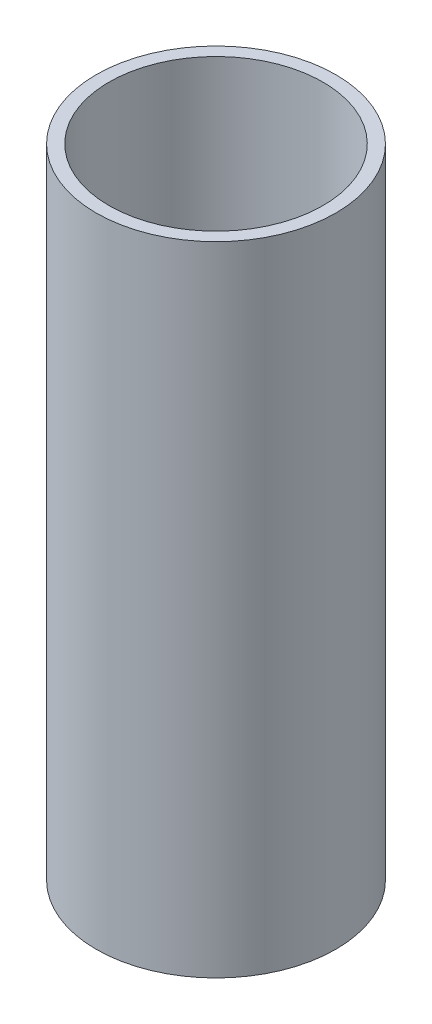
SolidWorks part; units mm, degrees
ref_plane "Front Plane" through (0, 0, 0) normal (0, 0, 1) x (1, 0, 0)
ref_plane "Top Plane" through (0, 0, 0) normal (0, 1, 0) x (1, 0, 0)
ref_plane "Right Plane" through (0, 0, 0) normal (1, 0, 0) x (0, 0, -1)
sketch "Sketch1" plane through (0, 0, 0) normal (0, 1, 0) x (1, 0, 0)
  circle A0 centre (0, 0) radius 14
  circle A1 centre (0, 0) radius 12.5
extrude "Boss-Extrude1" add sketch "Sketch1" along normal blind 74.498
